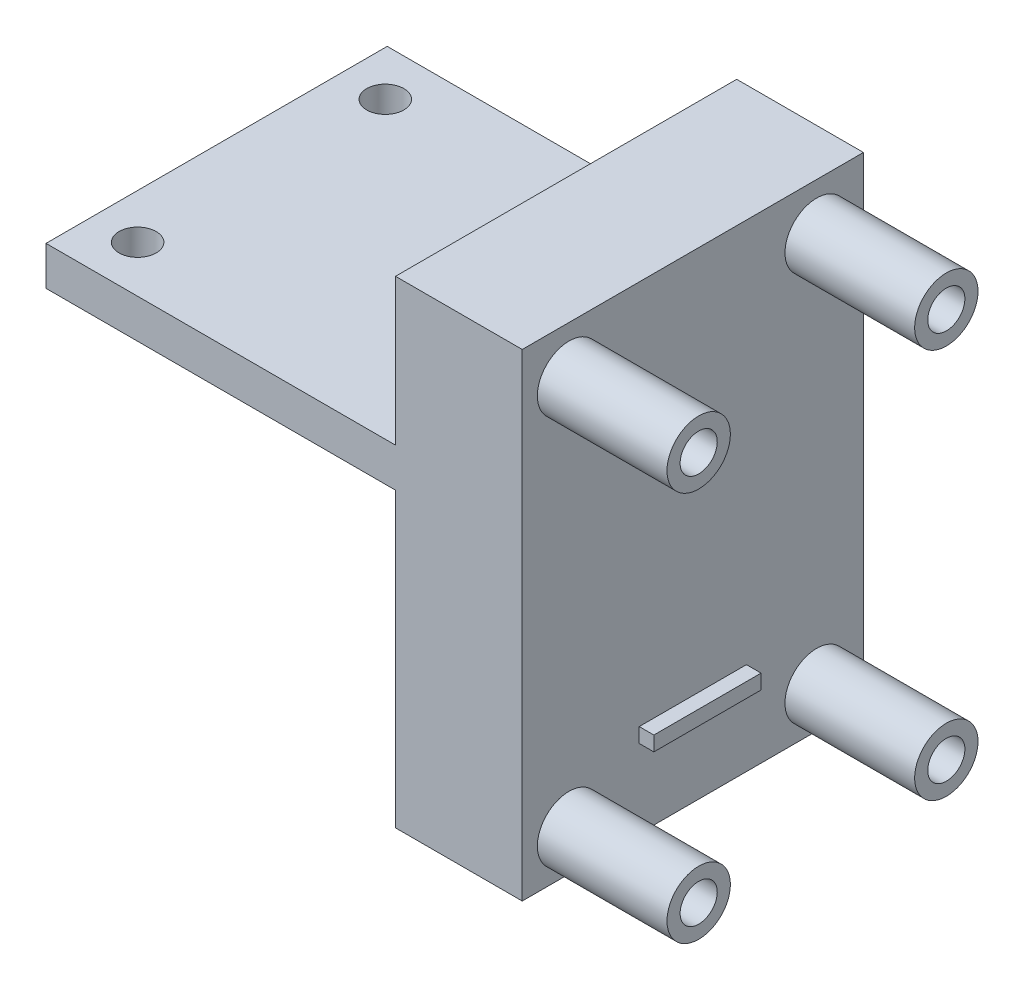
SolidWorks part; units mm, degrees
ref_plane "Front Plane" through (0, 0, 0) normal (0, 0, 1) x (1, 0, 0)
ref_plane "Top Plane" through (0, 0, 0) normal (0, 1, 0) x (1, 0, 0)
ref_plane "Right Plane" through (0, 0, 0) normal (1, 0, 0) x (0, 0, -1)
sketch "Sketch1" plane through (0, 0, 0) normal (0, 0, 1) x (1, 0, 0)
  line L0 (0, 0) -> (13, 0)
  line L1 (0, 0) -> (0, 30)
  line L2 (0, 30) -> (-35.85, 30)
  line L3 (-35.85, 30) -> (-35.85, 34)
  line L4 (-35.85, 34) -> (0, 34)
  line L5 (13, 34) -> (13, 0)
  line L6 (0, 34) -> (0, 49)
  line L7 (0, 49) -> (13, 49)
  line L8 (13, 49) -> (13, 34)
  dimension "D1" = 13
  dimension "D2" = 30
  dimension "D3" = 35.85
  dimension "D4" = 4
  dimension "D6" = 15
  dimension "D7" = 13
extrude "Boss-Extrude1" add sketch "Sketch1" against normal blind 35 contours L5 L0 L1 L2 L3 L4 L6 L7 L8
sketch "Sketch2" plane through (13, 0, 0) normal (1, 0, 0) x (0, 0, -1)
  line L0 (35, 0) -> (0, 0) construction
  line L1 (0, 49) -> (0, 0) construction
  line L2 (35, 49) -> (35, 0) construction
  circle A0 centre (4.8, 4.1) radius 1.905
  circle A1 centre (30.2, 4.1) radius 1.905
  point P12 (0, 0)
  dimension "D1" = 3.81
  dimension "D2" = 3.81
  dimension "D3" = 4.1
  dimension "D4" = 4.8
  dimension "D5" = 4.8
  dimension "D6" = 4.1
sketch "Sketch5" plane through (0, 34, 0) normal (0, 1, 0) x (1, 0, 0)
  line L0 (-35.85, 0) -> (0, 0) construction
  line L1 (-35.85, 35) -> (-35.85, 0) construction
  line L2 (-35.85, 35) -> (0, 35) construction
  circle A0 centre (-31.25, 4.8) radius 1.905
  circle A1 centre (-31.25, 30.2) radius 1.905
  dimension "D5" = 3.81
  dimension "D6" = 3.81
  dimension "D1" = 4.8
  dimension "D2" = 4.6
  dimension "D3" = 4.6
  dimension "D4" = 4.8
extrude "Cut-Extrude1" cut sketch "Sketch5" against normal through all
extrude "Cut-Extrude2" cut sketch "Sketch2" against normal through all
sketch "Sketch7" plane through (13, 0, 0) normal (1, 0, 0) x (0, 0, -1)
  line L0 (12, 8) -> (23, 8)
  line L1 (23, 8) -> (23, 9.5)
  line L2 (23, 9.5) -> (12, 9.5)
  line L3 (12, 9.5) -> (12, 8)
  line L4 (35, 0) -> (0, 0) construction
  line L5 (0, 49) -> (0, 0) construction
  line L6 (35, 49) -> (35, 0) construction
  dimension "D1" = 8
  dimension "D2" = 1.5
  dimension "D3" = 12
  dimension "D4" = 12
extrude "Boss-Extrude3" add sketch "Sketch7" along normal blind 1.5
sketch "Sketch8" plane through (13, 0, 0) normal (1, 0, 0) x (0, 0, -1)
  line L0 (35, 49) -> (0, 49) construction
  line L1 (0, 49) -> (0, 0) construction
  line L2 (35, 49) -> (35, 0) construction
  circle A0 centre (4.8, 44.1) radius 1.905
  circle A1 centre (30.2, 44.1) radius 1.905
  dimension "D1" = 3.81
  dimension "D2" = 3.81
  dimension "D3" = 4.9
  dimension "D4" = 4.8
  dimension "D5" = 4.8
  dimension "D6" = 4.9
extrude "Cut-Extrude3" cut sketch "Sketch8" against normal through all
sketch "Sketch11" plane through (13, 0, 0) normal (1, 0, 0) x (0, 0, -1)
  circle A0 centre (4.8, 44.1) radius 3.25
  circle A1 centre (30.2, 44.1) radius 3.25
  circle A2 centre (30.2, 4.1) radius 3.25
  circle A3 centre (4.8, 4.1) radius 3.25
  circle A4 centre (4.8, 44.1) radius 1.905 construction
  circle A5 centre (30.2, 44.1) radius 1.905 construction
  circle A6 centre (30.2, 4.1) radius 1.905 construction
  circle A7 centre (4.8, 4.1) radius 1.905 construction
  circle A8 centre (4.8, 44.1) radius 1.905
  circle A9 centre (30.2, 44.1) radius 1.905
  circle A10 centre (4.8, 4.1) radius 1.905
  circle A11 centre (30.2, 4.1) radius 1.905
  point P24 (6.2735, 35.9597)
  dimension "D1" = 6.5
  dimension "D2" = 6.5
  dimension "D3" = 6.5
  dimension "D4" = 6.5
  dimension "D5" = 3.81
  dimension "D6" = 3.81
  dimension "D7" = 3.81
  dimension "D8" = 3.81
extrude "Boss-Extrude4" add sketch "Sketch11" along normal blind 13.3
